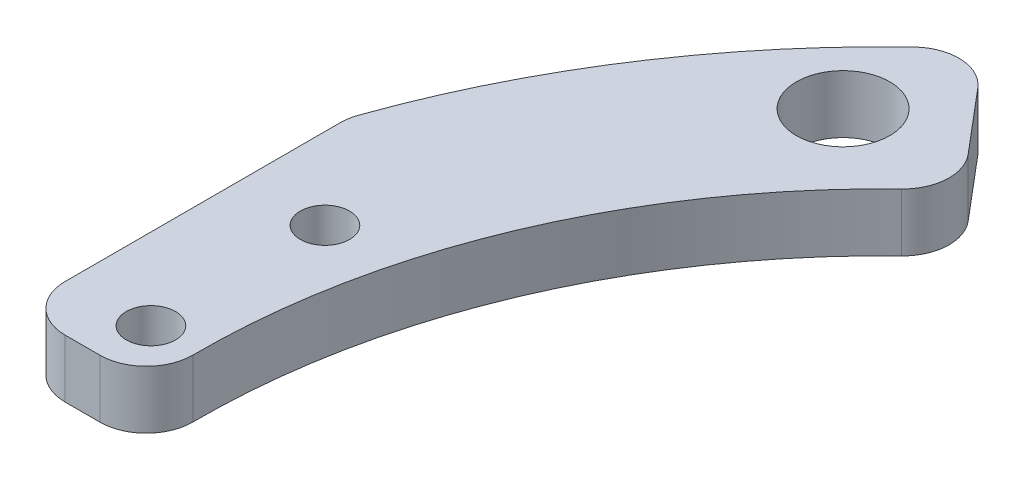
SolidWorks part; units mm, degrees
ref_plane "Front Plane" through (0, 0, 0) normal (0, 0, 1) x (1, 0, 0)
ref_plane "Top Plane" through (0, 0, 0) normal (0, 1, 0) x (1, 0, 0)
ref_plane "Right Plane" through (0, 0, 0) normal (1, 0, 0) x (0, 0, -1)
sketch "Sketch1" plane through (0, 0, 0) normal (0, 1, 0) x (1, 0, 0)
  line L0 (0, 0) -> (-63, 0) construction
  line L1 (-47.7573, 56.5264) -> (-38.0768, 45.0684)
  line L2 (0, 0) -> (-49.3664, 46.0349) construction
  line L15 (-63, -30) -> (-63, 30) construction
  line L16 (-55.5, 0) -> (-70.5, 0) construction
  line L17 (-70.4495, -22.6467) -> (-56.1692, -18.0562)
  circle A0 centre (0, 0) radius 55 construction
  circle A1 centre (0, 0) radius 62.5 construction
  circle A2 centre (-49.3664, 46.0349) radius 3.75 construction
  circle A5 centre (-49.3664, 46.0349) radius 4.025
  circle A7 centre (-63, 0) radius 2.125
  circle A8 centre (-63, -15) radius 2.125
  circle A9 centre (-63, 15) radius 2.125
  arc A10 (-38.0768, 45.0684) -> (-56.1692, -18.0562) centre (0, 0) ccw
  arc A11 (-47.7573, 56.5264) -> (-70.4495, -22.6467) centre (0, 0) ccw
  point P7 (-63, 0)
  dimension "D1" = 110
  dimension "D4" = 125
  dimension "D5" = 7.5
  dimension "D11" = 15
  dimension "D12" = 15
  dimension "D13" = 8.05
  dimension "D8" = 4.25
  dimension "D10" = 5
  dimension "D2" = 59
  dimension "D9" = 15
  dimension "D14" = 8
  dimension "D3" = 63
  dimension "D6" = 67.5
  dimension "D7" = 43
extrude "Boss-Extrude1" add sketch "Sketch1" along normal blind 5
sketch "Sketch2" plane through (0, 5, 0) normal (0, 1, 0) x (1, 0, 0)
  line L0 (0, 0) -> (-84.4523, 0) construction
  line L2 (-70, 27.6661) -> (-98.9046, 27.6661)
  line L3 (-70, 27.6661) -> (-70, -27.6661)
  line L4 (-70, -27.6661) -> (-98.9046, -27.6661)
  line L5 (-98.9046, 27.6661) -> (-98.9046, -27.6661)
  line L6 (-84.4523, -27.6661) -> (-84.4523, 27.6661) construction
  line L7 (-70, 0) -> (-98.9046, 0) construction
  dimension "D1" = 70
extrude "Cut-Extrude1" cut sketch "Sketch2" against normal through all both and the other way through all
sketch "Sketch3" plane through (0, 5, 0) normal (0, 1, 0) x (1, 0, 0)
  line L0 (-70, -22.5022) -> (-70, 24) construction
  line L1 (-70, -4.3988) -> (-45.7929, -4.3988)
  line L2 (-70, -4.3988) -> (-70, -25.4993)
  line L3 (-70, -25.4993) -> (-45.7929, -25.4993)
  line L4 (-45.7929, -4.3988) -> (-45.7929, -25.4993)
  line L5 (-57.8964, -25.4993) -> (-57.8964, -4.3988) construction
  line L6 (-70, -14.949) -> (-45.7929, -14.949) construction
  point P56 (-57.8964, -14.949)
extrude "Cut-Extrude2" cut sketch "Sketch3" against normal through all both and the other way through all
fillet "Fillet1" radius 4 5 edges at (-70, 2.5, -24) (-70, 2.5, 4.3988) (-58.8358, 2.5, 4.3988) (-38.0768, 2.5, -45.0684) (-47.7573, 2.5, -56.5264)
sketch "Sketch4" plane through (0, 0, 0) normal (0, 1, 0) x (1, 0, 0)
  circle A0 centre (0, 0) radius 33.3124
